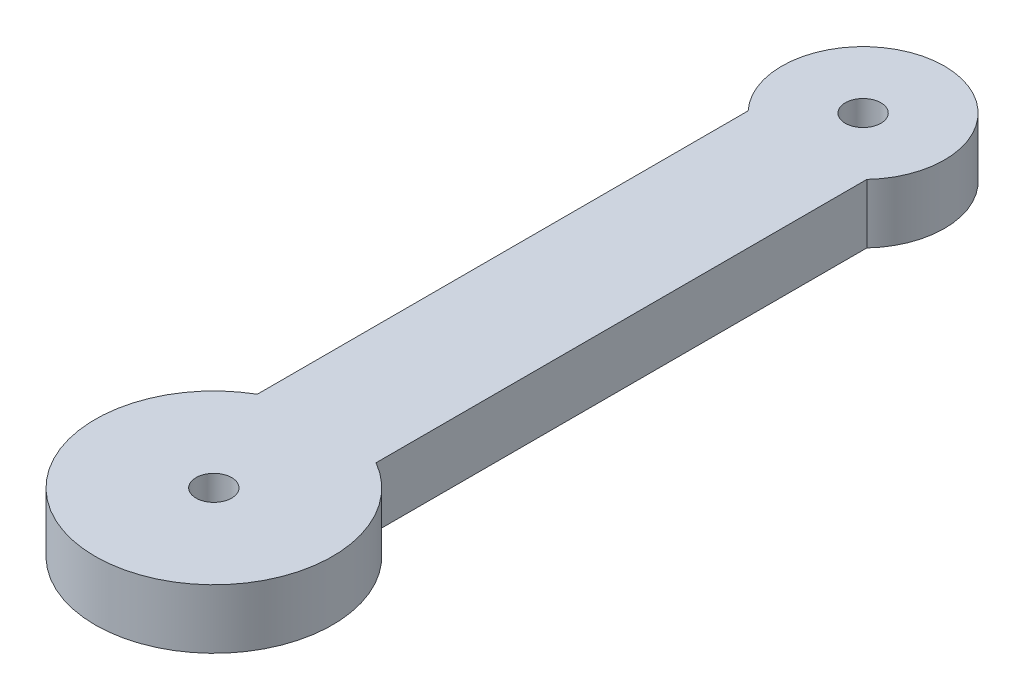
SolidWorks part; units mm, degrees
ref_plane "Front Plane" through (0, 0, 0) normal (0, 0, 1) x (1, 0, 0)
ref_plane "Top Plane" through (0, 0, 0) normal (0, 1, 0) x (1, 0, 0)
ref_plane "Right Plane" through (0, 0, 0) normal (1, 0, 0) x (0, 0, -1)
sketch "Sketch2" plane through (0, 0, 0) normal (0, 1, 0) x (1, 0, 0)
  line L0 (-2.5, 25) -> (-2.5, 4.3301)
  line L1 (2.5, 25) -> (2.5, 4.3301)
  circle A0 centre (0, 0) radius 0.75
  arc A1 (-2.5, 4.3301) -> (2.5, 4.3301) centre (0, 0) ccw
  circle A2 centre (0, 27.3428) radius 0.75
  arc A3 (2.5, 25) -> (-2.5, 25) centre (0, 27.3428) ccw
  dimension "D1" = 1.5
  dimension "D2" = 5
  dimension "D3" = 3.4261
  dimension "D4" = 2.5
  dimension "D5" = 25
extrude "Boss-Extrude1" add sketch "Sketch2" along normal blind 2.5
